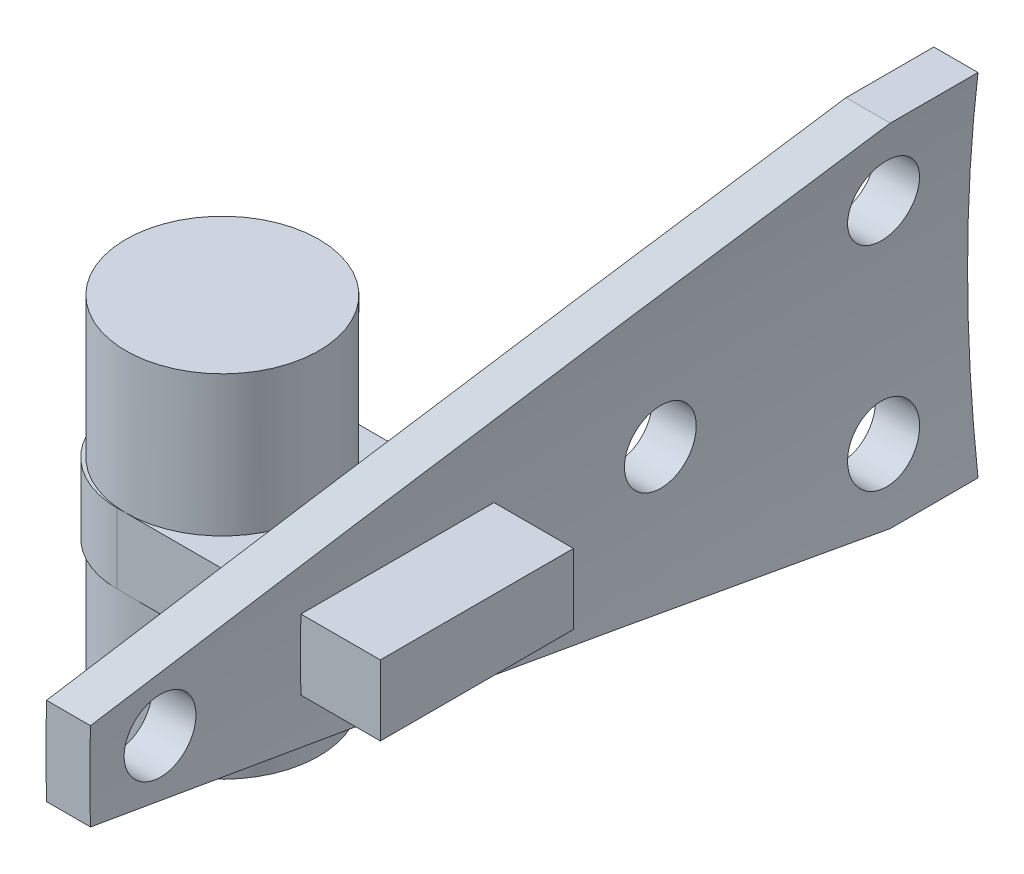
SolidWorks part; units mm, degrees
material "Plain Carbon Steel"
ref_plane "Front Plane" through (0, 0, 0) normal (0, 0, 1) x (1, 0, 0)
ref_plane "Top Plane" through (0, 0, 0) normal (0, 1, 0) x (1, 0, 0)
ref_plane "Right Plane" through (0, 0, 0) normal (1, 0, 0) x (0, 0, -1)
sketch "Sketch1" plane through (0, 0, 0) normal (0, 0, 1) x (1, 0, 0)
  line L0 (0, 0) -> (-52.4035, 0) construction
  line L1 (-86.4737, 10) -> (-83.9566, 10)
  line L2 (-86.4737, -10) -> (-83.9566, -10)
  arc A0 (-83.9566, 10) -> (-83.9566, -10) centre (0, 0) ccw
  arc A1 (-86.4737, 10) -> (-86.4737, -10) centre (0, 0) ccw
  dimension "D2" = 84.55
  dimension "D1" = 2.5
  dimension "D3" = 20
extrude "Boss-Extrude1" add sketch "Sketch1" along normal blind 50
sketch "Sketch2" plane through (0, 0, 0) normal (1, 0, 0) x (0, 0, -1)
  line L0 (0, 10) -> (0, -10)
  line L1 (0, 10) -> (-50, 10) construction
  line L2 (0, 10) -> (0, -10) construction
  line L3 (0, -10) -> (-50, -10) construction
  line L4 (-50, 10) -> (-50, -10) construction
  line L5 (0, -10) -> (-5, -10)
  line L6 (-5, -10) -> (-50, -2.5)
  line L7 (-50, -2.5) -> (-50, 2.5)
  line L8 (-50, 2.5) -> (-5, 10)
  line L9 (-5, 10) -> (0, 10)
  line L10 (0, 0) -> (-50.031, 0) construction
  line L12 (-88.7937, 27.6855) -> (20.3533, 27.6855)
  line L13 (-88.7937, 27.6855) -> (-88.7937, -33.0502)
  line L14 (-88.7937, -33.0502) -> (20.3533, -33.0502)
  line L15 (20.3533, 27.6855) -> (20.3533, -33.0502)
  dimension "D1" = 5
extrude "Cut-Extrude1" cut sketch "Sketch2" against normal through all
hole_wizard "#20 (0.161) Diameter Hole1" positions "Sketch5" profile "Sketch4" hole size "#20" standard "ANSI Inch"
sketch "Sketch5" plane through (0, 0, 0) normal (1, 0, 0) x (0, 0, -1)
  line L1 (0, -10) -> (-42.3856, -10)
  line L2 (0, -10) -> (0, 10)
  line L3 (0, 10) -> (-42.3856, 10)
  line L4 (-42.3856, -10) -> (-42.3856, 10)
  line L7 (-5, 10) -> (0, 10) construction
  line L8 (0, 0) -> (-42.3856, 0)
  line L10 (-5, 6) -> (-5, -6)
  line L11 (-50, 2.5) -> (-50, -2.5) construction
  point P0 (-46, 0)
  point P164 (-5, 6)
  point P165 (-5, -6)
  point P172 (-5, 0)
  point P177 (-17.5, 0)
  dimension "D1" = 5
  dimension "D2" = 4
  dimension "D3" = 4
  dimension "D4" = 12.5
sketch "Sketch4" plane through (0, 0, 46) normal (0, 1, 0) x (0, 0, -1)
  line L0 (0, 0) -> (0, 87.05)
  line L1 (0, 87.05) -> (2.0447, 87.05)
  line L2 (2.0447, 87.05) -> (2.0447, 0)
  line L5 (2.0447, 0) -> (0, 0)
  line L11 (0, -6.35) -> (0, 107.95) construction
  dimension "Thru Hole Dia." = 4.0894
  dimension "Thru Hole Depth" = 87.05
ref_plane "Plane1" through (-80, 0, 0) normal (1, 0, 0) x (0, 0, -1)
sketch "Sketch7" plane through (-80, 0, -87.9998) normal (1, 0, 0) x (0, 0, -1)
  line L0 (-87.9998, 0) -> (-80.3469, 0) construction
  line L1 (-125.9998, 2) -> (-114.9998, 2)
  line L2 (-125.9998, 2) -> (-125.9998, -2)
  line L3 (-125.9998, -2) -> (-114.9998, -2)
  line L4 (-114.9998, 2) -> (-114.9998, -2)
  line L5 (-87.9998, 10) -> (-87.9998, -10) construction
  line L6 (-87.9998, -10) -> (-87.9998, 10) construction
  circle A2 centre (-133.9998, 0) radius 2.0447 construction
  point P8 (-125.9998, 0)
  dimension "D2" = 11
  dimension "D1" = 4
  dimension "D3" = 8
extrude "Boss-Extrude2" add sketch "Sketch7" against normal blind 20
fillet "Fillet1" radius 2 4 edges at (-87.027, 2, 32.5) (-87.05, 0, 38) (-87.05, 0, 27) (-87.027, -2, 32.5)
sketch "Sketch8" plane through (0, -2, 0) normal (0, -1, 0) x (1, 0, 0)
  line L1 (-89, 27) -> (-100, 27) construction
  line L2 (-89, 27) -> (-89, 38) construction
  line L3 (-89, 38) -> (-100, 38) construction
  line L4 (-100, 27) -> (-100, 38) construction
  line L5 (-89, 27) -> (-100, 38) construction
  line L6 (-89, 38) -> (-100, 27) construction
  circle A0 centre (-94.5, 32.5) radius 5.5
  point P0 (-94.5, 32.5)
extrude "Boss-Extrude3" add sketch "Sketch8" along normal blind 8 and the other way blind 12
fillet "Fillet2" radius 5 2 edges at (-100, 0, 38) (-100, 0, 27)
equation "\"TubeDiameter\" = 6.500in"
equation "\"D2@Sketch1\"=\"TubeDiameter\"/2+2mm"
